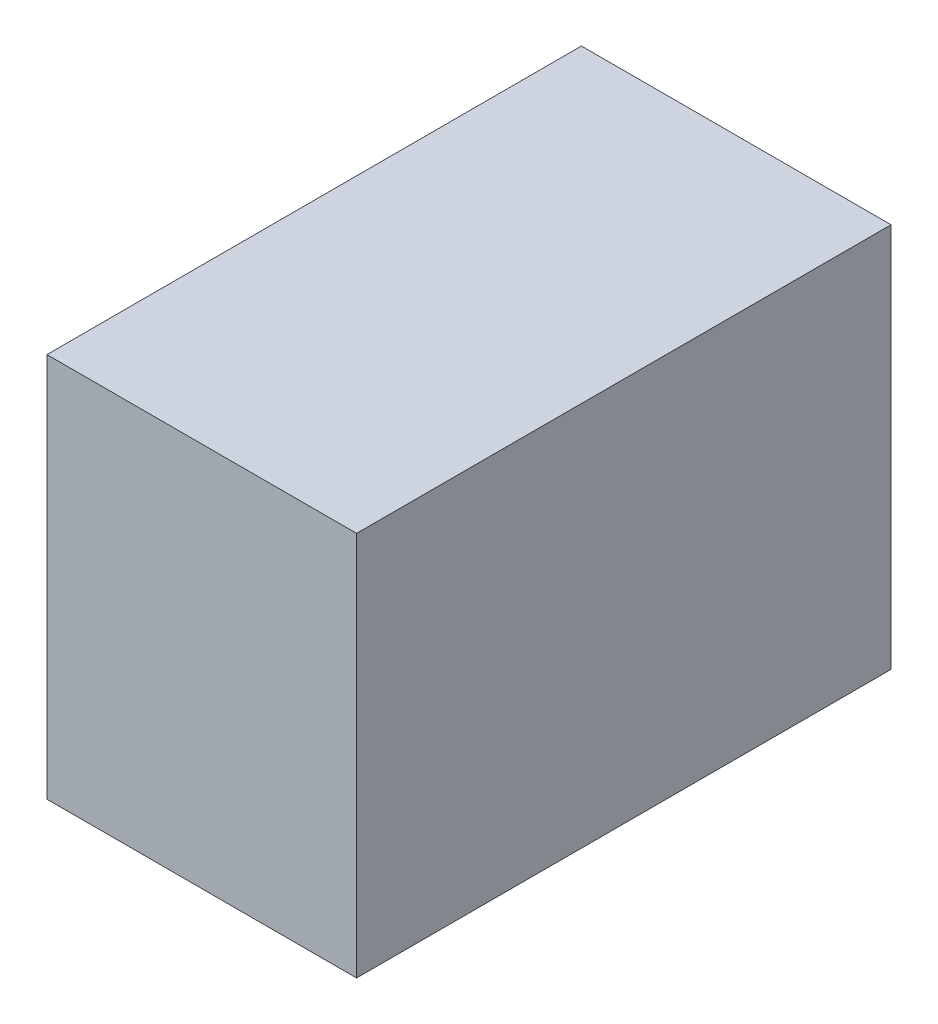
SolidWorks part; units mm, degrees
ref_plane "Front Plane" through (0, 0, 0) normal (0, 0, 1) x (1, 0, 0)
ref_plane "Top Plane" through (0, 0, 0) normal (0, 1, 0) x (1, 0, 0)
ref_plane "Right Plane" through (0, 0, 0) normal (1, 0, 0) x (0, 0, -1)
sketch "Sketch2" plane through (0, 0, 0) normal (0, 1, 0) x (1, 0, 0)
  line L1 (-201.0289, -347.0148) -> (201.0289, -347.0148)
  line L2 (-201.0289, -347.0148) -> (-201.0289, 347.0148)
  line L3 (-201.0289, 347.0148) -> (201.0289, 347.0148)
  line L4 (201.0289, -347.0148) -> (201.0289, 347.0148)
  line L5 (-201.0289, -347.0148) -> (201.0289, 347.0148) construction
  line L6 (-201.0289, 347.0148) -> (201.0289, -347.0148) construction
  point P0 (0, 0)
extrude "Boss-Extrude1" add sketch "Sketch2" along normal blind 500
